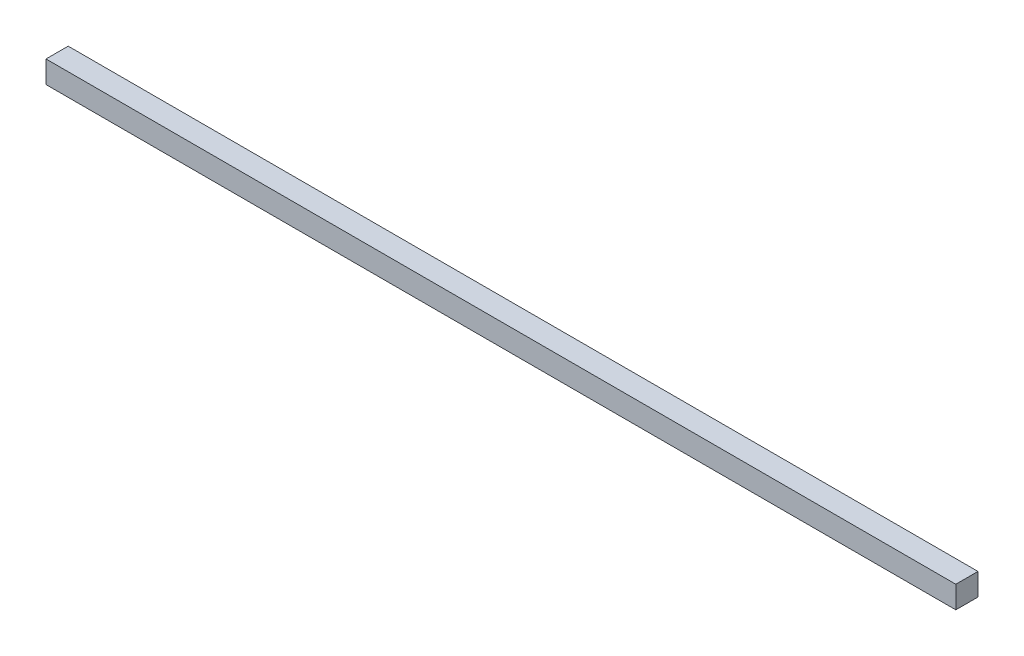
SolidWorks part; units mm, degrees
ref_plane "Front Plane" through (0, 0, 0) normal (0, 0, 1) x (1, 0, 0)
ref_plane "Top Plane" through (0, 0, 0) normal (0, 1, 0) x (1, 0, 0)
ref_plane "Right Plane" through (0, 0, 0) normal (1, 0, 0) x (0, 0, -1)
sketch "Sketch1" plane through (0, 0, 0) normal (0, 1, 0) x (1, 0, 0)
  line L0 (-205, 5) -> (205, -5) construction
  line L1 (-205, 5) -> (205, 5)
  line L2 (-205, 5) -> (-205, -5)
  line L3 (-205, -5) -> (205, -5)
  line L4 (205, 5) -> (205, -5)
  dimension "D1" = 410
  dimension "D2" = 10
extrude "Boss-Extrude1" add sketch "Sketch1" along normal blind 10
